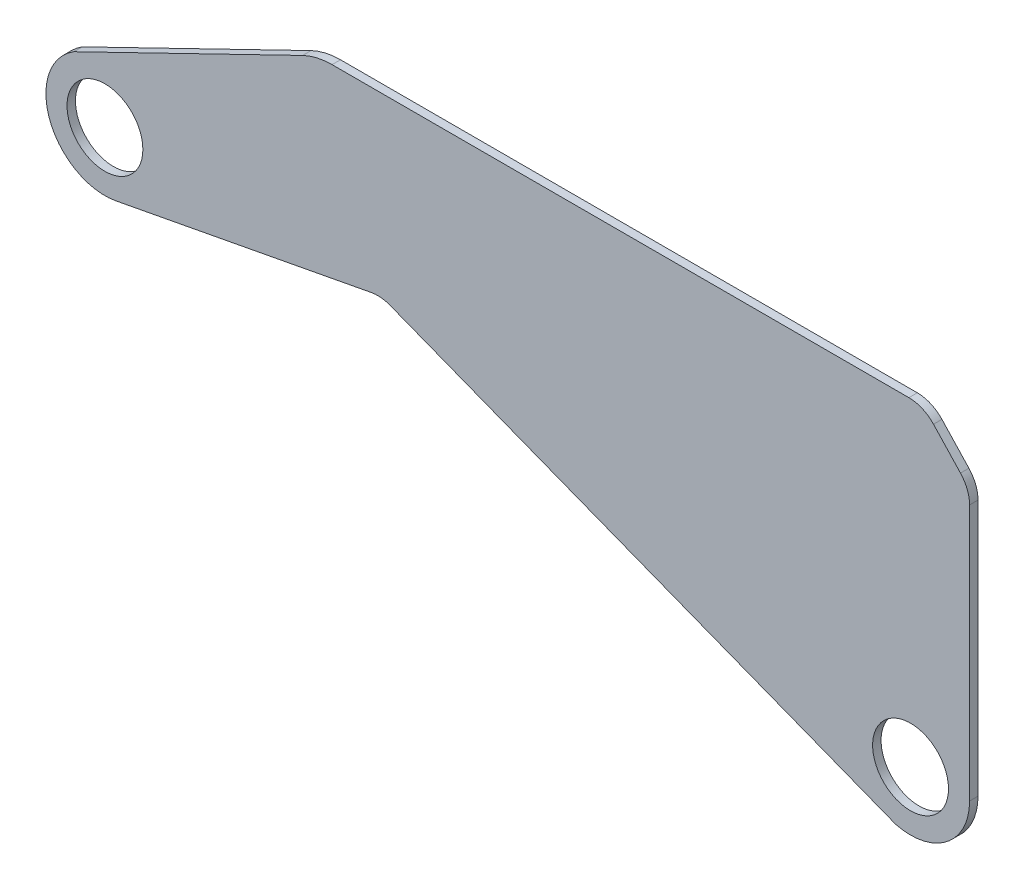
SolidWorks part; units mm, degrees
material "ABS PC"
ref_plane "Front Plane" through (0, 0, 0) normal (0, 0, 1) x (1, 0, 0)
ref_plane "Top Plane" through (0, 0, 0) normal (0, 1, 0) x (1, 0, 0)
ref_plane "Right Plane" through (0, 0, 0) normal (1, 0, 0) x (0, 0, -1)
sketch "Sketch1" plane through (0, 0, 0) normal (0, 0, 1) x (1, 0, 0)
  line L0 (22.225, 0) -> (22.225, 101.6)
  line L1 (22.225, 101.6) -> (4.8791, 120.1548)
  line L2 (4.8791, 120.1548) -> (-223.7209, 120.1548)
  line L3 (-223.7209, 120.1548) -> (-315.1072, 75.7575)
  line L4 (-299.299, 35.0094) -> (-199.4699, 53.8962)
  line L5 (-199.4699, 53.8962) -> (-5.519, -21.5288)
  circle A0 centre (0, 0) radius 14.2875
  arc A1 (-5.519, -21.5288) -> (22.225, 0) centre (0, 0) ccw
  arc A2 (-311.0787, 77.7146) -> (-299.299, 35.0094) centre (-303.4304, 56.8471) ccw
  circle A3 centre (-303.4304, 56.8471) radius 14.2875
  point P3 (-7.6165, -20.9051)
  point P4 (-5.519, -21.5288)
  point P16 (0, 0)
  point P17 (22.2249, 0)
  dimension "D1" = 28.575
  dimension "D2" = 44.45
  dimension "D7" = 44.45
  dimension "D9" = 28.575
  dimension "D3" = 101.6
  dimension "D4" = 25.4
  dimension "D5" = 228.6
  dimension "D6" = 101.6
  dimension "D8" = 101.6
extrude "Boss-Extrude1" add sketch "Sketch1" along normal blind 3.175 contours L3 A2 L4 L5 A1 L0 L1 L2 A3 A0
fillet "Fillet1" radius 12.7 1 edges at (-199.4699, 53.8962, 1.5875)
fillet "Fillet2" radius 25.4 1 edges at (-223.7209, 120.1548, 1.5875)
fillet "Fillet3" radius 12.7 1 edges at (22.225, 101.6, 1.5875)
fillet "Fillet4" radius 12.7 1 edges at (4.8791, 120.1548, 1.5875)
